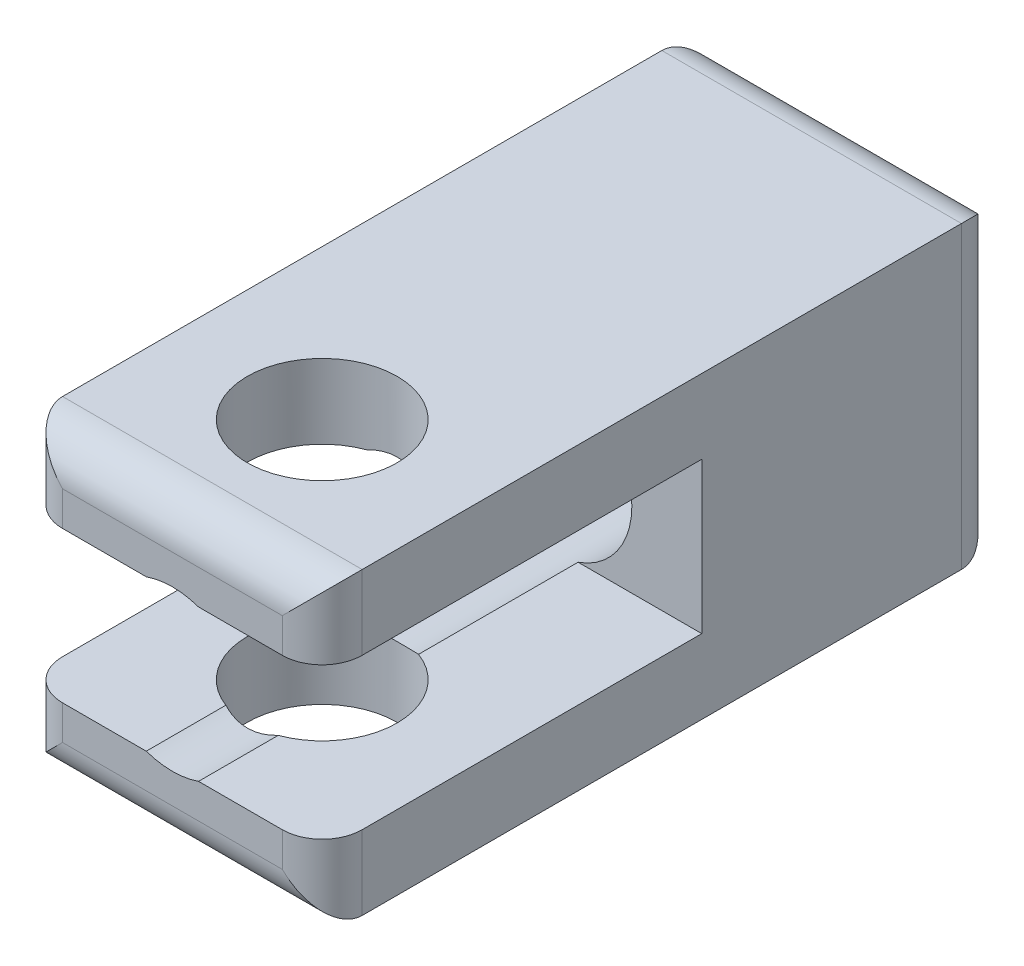
SolidWorks part; units mm, degrees
ref_plane "Front" through (0, 0, 0) normal (0, 0, 1) x (1, 0, 0)
ref_plane "Top" through (0, 0, 0) normal (0, 1, 0) x (1, 0, 0)
ref_plane "Right" through (0, 0, 0) normal (1, 0, 0) x (0, 0, -1)
sketch "Sketch1" plane through (0, 0, 0) normal (0, 0, 1) x (1, 0, 0)
  line L1 (0, 0) -> (19.05, 0)
  line L2 (0, 0) -> (0, 19.05)
  line L3 (0, 19.05) -> (19.05, 19.05)
  line L4 (19.05, 0) -> (19.05, 19.05)
  line L5 (0, 0) -> (19.05, 19.05) construction
  line L6 (0, 19.05) -> (19.05, 0) construction
  point P4 (9.525, 9.525)
  dimension "D1" = 19.05
extrude "Boss-Extrude1" add sketch "Sketch1" along normal blind 43.18
fillet "Fillet1" radius 2.54 8 edges at (9.525, 0, 0) (19.05, 9.525, 0) (9.525, 19.05, 0) (0, 9.525, 0) (9.525, 19.05, 43.18) (19.05, 9.525, 43.18) (9.525, 0, 43.18) (0, 9.525, 43.18)
sketch "Sketch2" plane through (0, 0, 0) normal (0, 0, -1) x (-1, 0, 0)
  line L0 (-16.51, 16.51) -> (-2.54, 2.54) construction
  circle A0 centre (-9.525, 9.525) radius 5.08
  dimension "D1" = 10.16
extrude "Cut-Extrude1" cut sketch "Sketch2" against normal up to next
sketch "Sketch3" plane through (19.05, 0, 0) normal (1, 0, 0) x (0, 0, -1)
  line L0 (-40.64, 19.05) -> (-40.64, 0) construction
  line L1 (-62.23, 4.7244) -> (-19.05, 4.7244)
  line L2 (-62.23, 4.7244) -> (-62.23, 14.3256)
  line L3 (-62.23, 14.3256) -> (-19.05, 14.3256)
  line L4 (-19.05, 4.7244) -> (-19.05, 14.3256)
  line L5 (-62.23, 4.7244) -> (-19.05, 14.3256) construction
  line L6 (-62.23, 14.3256) -> (-19.05, 4.7244) construction
  line L7 (-40.64, 19.05) -> (-2.54, 19.05) construction
  line L8 (0, 16.51) -> (0, 2.54) construction
  point P0 (-40.64, 9.525)
  dimension "D1" = 4.7244
  dimension "D2" = 19.05
extrude "Cut-Extrude2" cut sketch "Sketch3" against normal through all
sketch "Sketch4" plane through (0, 0, 0) normal (0, -1, 0) x (1, 0, 0)
  line L0 (2.54, 43.18) -> (16.51, 43.18) construction
  line L1 (2.54, 43.18) -> (16.51, 43.18) construction
  line L2 (9.525, 43.18) -> (9.525, 33.655) construction
  circle A0 centre (9.525, 33.655) radius 4.7625
  dimension "D2" = 9.525
  dimension "D1" = 9.525
extrude "Cut-Extrude3" cut sketch "Sketch4" against normal through all
